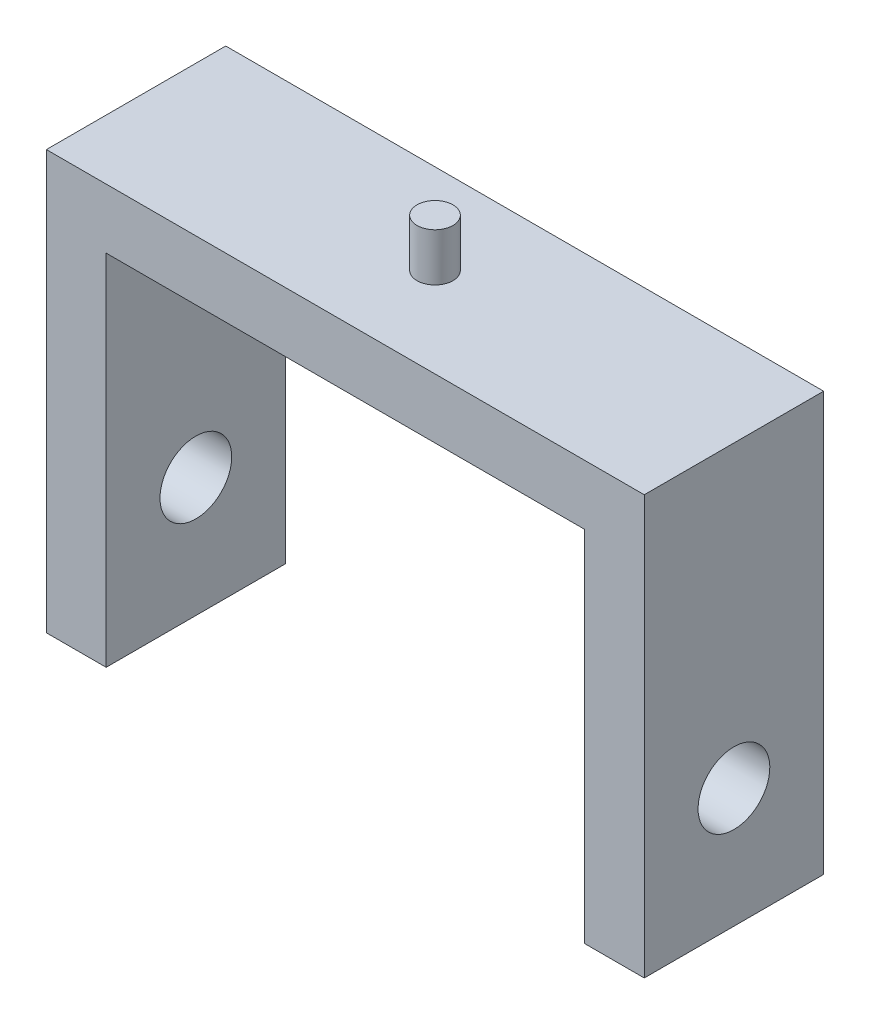
SolidWorks part; units mm, degrees
ref_plane "Front Plane" through (0, 0, 0) normal (0, 0, 1) x (1, 0, 0)
ref_plane "Top Plane" through (0, 0, 0) normal (0, 1, 0) x (1, 0, 0)
ref_plane "Right Plane" through (0, 0, 0) normal (1, 0, 0) x (0, 0, -1)
sketch "Sketch1" plane through (0, 0, 0) normal (0, 0, 1) x (1, 0, 0)
  line L1 (-20, 15) -> (20, 15)
  line L2 (-20, 15) -> (-20, -15)
  line L4 (20, 15) -> (20, -15)
  line L5 (-20, 15) -> (20, -15) construction
  line L6 (-20, -15) -> (20, 15) construction
  point P0 (0, 0)
  dimension "D1" = 40
  dimension "D2" = 30
extrude "Extrude-Thin1" add sketch "Sketch1" along normal mid plane 15 thin thin type one direction wall 5
sketch "Sketch2" plane through (0, 20, 0) normal (0, 1, 0) x (1, 0, 0)
  circle A0 centre (0, 0) radius 1.5
  dimension "D1" = 3
extrude "Boss-Extrude1" add sketch "Sketch2" along normal blind 4
sketch "Sketch3" plane through (25, 0, 0) normal (1, 0, 0) x (0, 0, -1)
  line L0 (-7.5, -15) -> (7.5, -15) construction
  circle A0 centre (0, -5) radius 3
  point P3 (0, 0)
  dimension "D1" = 6
  dimension "D2" = 10
extrude "Cut-Extrude1" cut sketch "Sketch3" against normal through all both and the other way through all
